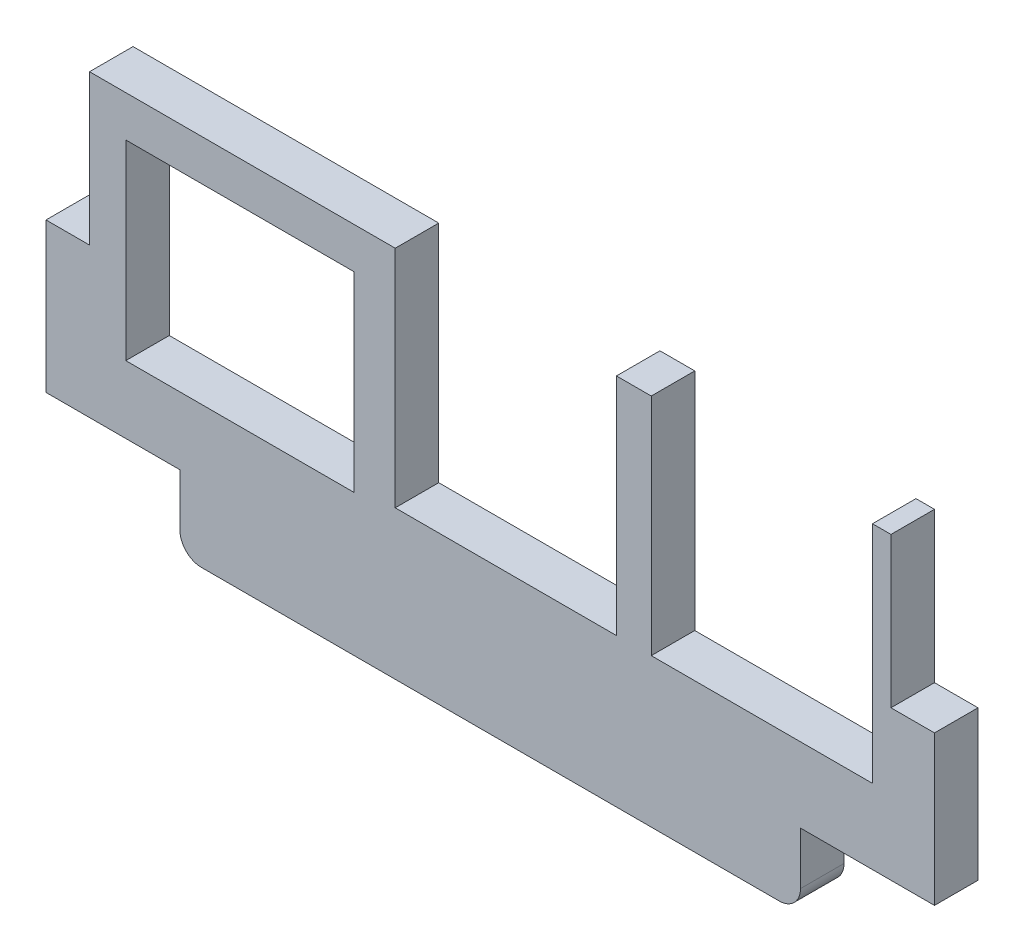
SolidWorks part; units mm, degrees
ref_plane "Front Plane" through (0, 0, 0) normal (0, 0, 1) x (1, 0, 0)
ref_plane "Top Plane" through (0, 0, 0) normal (0, 1, 0) x (1, 0, 0)
ref_plane "Right Plane" through (0, 0, 0) normal (1, 0, 0) x (0, 0, -1)
sketch "Model" plane through (0, 0, 0) normal (0, 0, 1) x (1, 0, 0)
  line L340 (5.588, 23.2802) -> (21.59, 23.2802)
  line L341 (3.048, 15.6348) -> (0, 15.6348)
  line L342 (3.048, 26.1504) -> (3.048, 15.6348)
  line L343 (5.588, 9.8944) -> (5.588, 23.2802)
  line L344 (21.59, 9.8944) -> (5.588, 9.8944)
  line L345 (21.59, 23.2802) -> (21.59, 9.8944)
  line L346 (24.4602, 26.1504) -> (3.048, 26.1504)
  line L347 (24.4602, 10.4024) -> (24.4602, 26.1504)
  line L348 (39.9542, 10.4024) -> (24.4602, 10.4024)
  line L349 (39.9542, 26.1504) -> (39.9542, 10.4024)
  line L350 (42.3926, 26.1504) -> (39.9542, 26.1504)
  line L351 (42.3926, 10.4024) -> (42.3926, 26.1504)
  line L352 (57.8866, 10.4024) -> (42.3926, 10.4024)
  line L353 (57.8866, 26.1504) -> (57.8866, 10.4024)
  line L354 (59.182, 26.1504) -> (57.8866, 26.1504)
  line L355 (59.182, 15.6348) -> (59.182, 26.1504)
  line L356 (62.23, 15.6348) -> (59.182, 15.6348)
  line L357 (62.23, 5.17) -> (62.23, 15.6348)
  line L358 (52.847, 5.17) -> (62.23, 5.17)
  line L359 (0, 5.17) -> (9.383, 5.17)
  line L360 (0, 15.6348) -> (0, 5.17)
  line L489 (9.383, 5.17) -> (9.383, 1.5)
  line L490 (52.847, 1.5) -> (52.847, 5.17)
  line L491 (10.883, 0) -> (51.347, 0)
  arc A76 (51.347, 0) -> (52.847, 1.5) centre (51.347, 1.5) ccw
  arc A77 (9.383, 1.5) -> (10.883, 0) centre (10.883, 1.5) ccw
extrude "Boss-Extrude1" add sketch "Model" along normal blind 3.048
